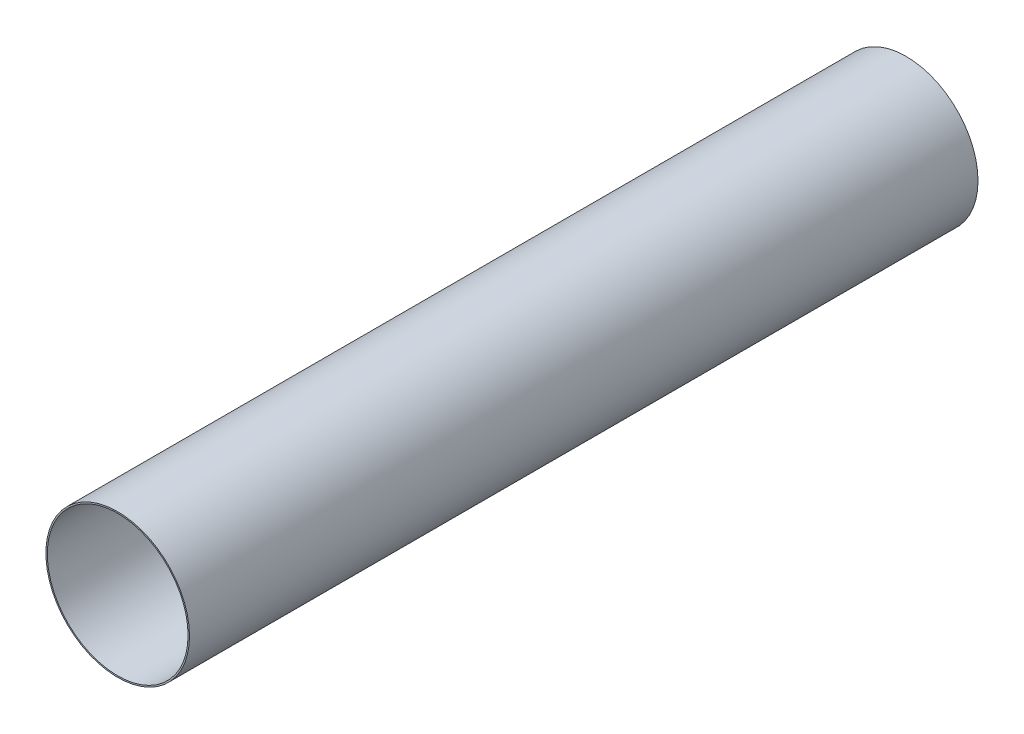
SolidWorks part; units mm, degrees
material "Thornel Mat VMA"
ref_plane "Front Plane" through (0, 0, 0) normal (0, 0, 1) x (1, 0, 0)
ref_plane "Top Plane" through (0, 0, 0) normal (0, 1, 0) x (1, 0, 0)
ref_plane "Right Plane" through (0, 0, 0) normal (1, 0, 0) x (0, 0, -1)
sketch "Sketch1" plane through (0, 0, 0) normal (0, 0, 1) x (1, 0, 0)
  circle A0 centre (0, 0) radius 32.385
  circle A1 centre (0, 0) radius 31.75
  dimension "D1" = 63.5
  dimension "D2" = 0.635
extrude "Boss-Extrude1" add sketch "Sketch1" along normal blind 355.6
